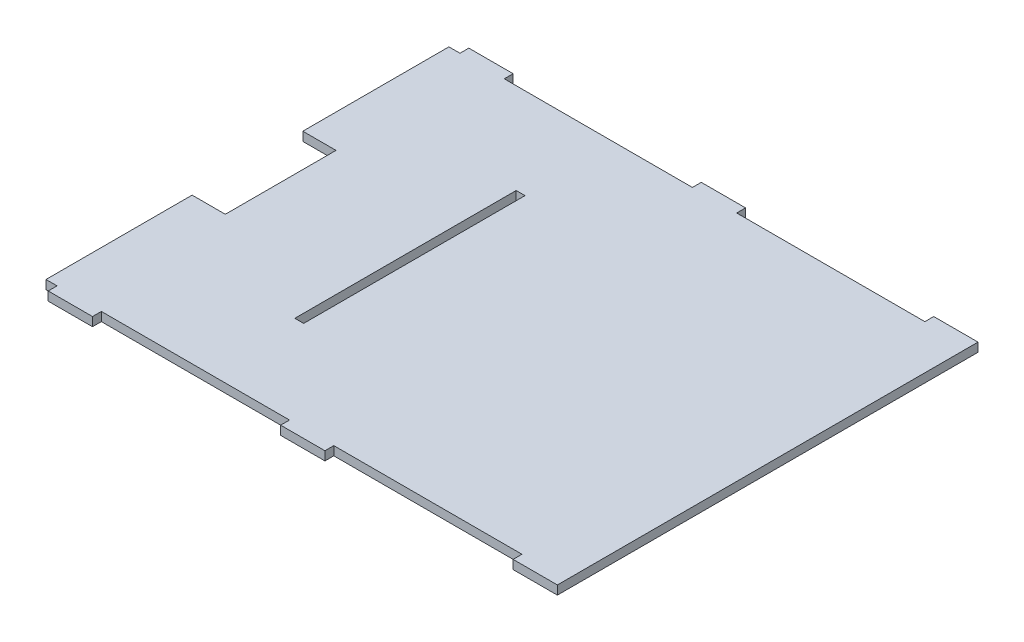
SolidWorks part; units mm, degrees
ref_plane "Front Plane" through (0, 0, 0) normal (0, 0, 1) x (1, 0, 0)
ref_plane "Top Plane" through (0, 0, 0) normal (0, 1, 0) x (1, 0, 0)
ref_plane "Right Plane" through (0, 0, 0) normal (1, 0, 0) x (0, 0, -1)
sketch "Sketch1" plane through (0, 0, 0) normal (0, 1, 0) x (1, 0, 0)
  line L0 (-112.5, -92) -> (-176.5239, -92) construction
  line L1 (-112.5, 94) -> (-92.5, 94)
  line L2 (-117.5, 90) -> (-117.5, -92)
  line L4 (117.5, 94) -> (117.5, -96)
  line L5 (-115.5525, 94.4089) -> (117.5, -96) construction
  line L6 (-117.5, -94) -> (117.5, 94) construction
  line L7 (-117.5, -92) -> (-112.5, -92)
  line L11 (-112.5, -92) -> (-112.5, -96)
  line L12 (-92.5, -96) -> (-92.5, -92)
  line L13 (-7.5, -92) -> (-7.5, -96)
  line L14 (12.5, -96) -> (12.5, -92)
  line L15 (97.5, -96) -> (97.5, -92)
  line L16 (-117.5, -1) -> (117.5, -1) construction
  line L18 (12.5, -96) -> (-7.5, -96)
  line L19 (-92.5, -96) -> (-112.5, -96)
  line L20 (12.5, -92) -> (97.5, -92)
  line L21 (-92.5, -92) -> (-7.5, -92)
  line L22 (97.5, -96) -> (117.5, -96)
  line L23 (97.5, 94) -> (97.5, 90)
  line L24 (12.5, 90) -> (97.5, 90)
  line L25 (12.5, 94) -> (12.5, 90)
  line L26 (-7.5, 90) -> (-7.5, 94)
  line L27 (-92.5, 94) -> (-92.5, 90)
  line L28 (-92.5, 90) -> (-7.5, 90)
  line L29 (-117.5, 90) -> (-112.5, 90)
  line L30 (-112.5, 90) -> (-112.5, 94)
  line L31 (-7.5, 94) -> (12.5, 94)
  line L32 (97.5, 94) -> (117.5, 94)
  line L33 (-42.11, 49) -> (-42.11, -51)
  line L34 (-46.11, 49) -> (-46.11, -51)
  line L37 (-42.11, -51) -> (-46.11, -51)
  line L38 (-46.11, 49) -> (-42.11, 49)
  point P0 (0, 0)
  point P32 (-44.11, -51)
  dimension "D1" = 159.61
  dimension "D2" = 235
  dimension "D3" = 4
  dimension "D4" = 100
  dimension "D5" = 50
  dimension "D6" = 20
  dimension "D7" = 182
  dimension "D8" = 4
  dimension "D9" = 85
  dimension "D10" = 5
  dimension "D11" = 20
  dimension "D12" = 85
extrude "Boss-Extrude1" add sketch "Sketch1" along normal blind 4 contours L28 L26 L31 L25 L24 L23 L32 L4 L22 L15 L20 L14 L18 L13 L21 L12 L19 L11 L7 L2 L29 L30 L1 L27 | L33 L37 L34 L38
sketch "Sketch2" plane through (0, 4, 0) normal (0, 1, 0) x (1, 0, 0)
  line L0 (-117.5, -1) -> (-61.9178, -1) construction
  line L1 (-117.5, 90) -> (-117.5, -92) construction
  line L3 (-132.5, -26) -> (-102.5, -26)
  line L4 (-132.5, -26) -> (-132.5, 24)
  line L5 (-132.5, 24) -> (-102.5, 24)
  line L6 (-102.5, -26) -> (-102.5, 24)
  line L7 (-132.5, -26) -> (-102.5, 24) construction
  line L8 (-132.5, 24) -> (-102.5, -26) construction
  dimension "D1" = 15
  dimension "D2" = 50
extrude "Cut-Extrude1" cut sketch "Sketch2" against normal blind 10
